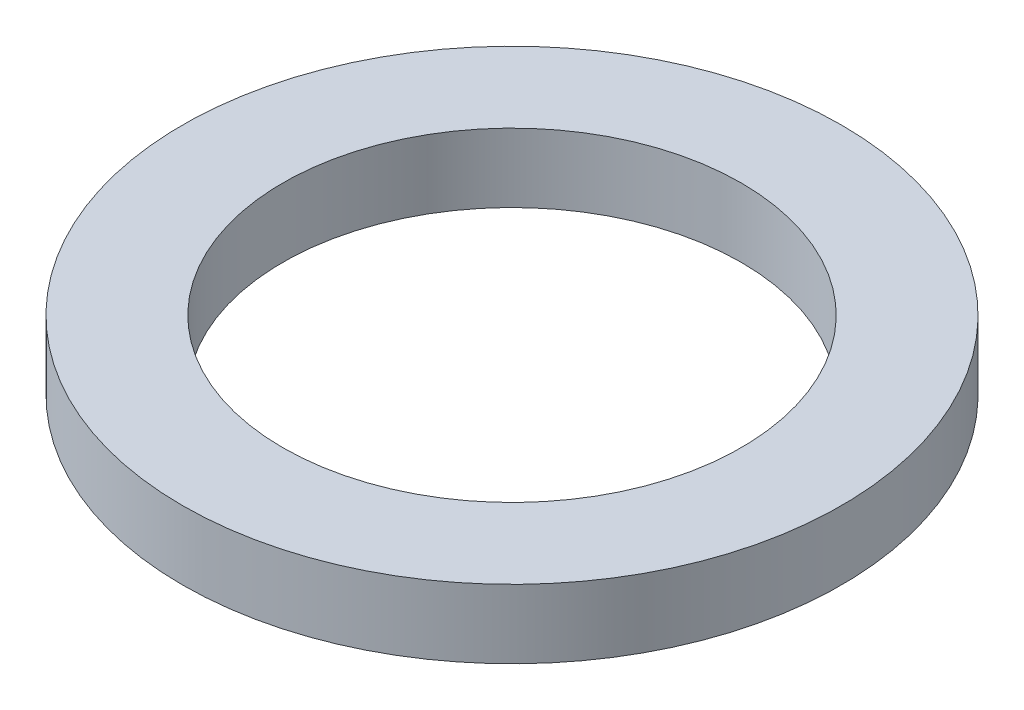
SolidWorks part; units mm, degrees
material "ABS"
ref_plane "Front Plane" through (0, 0, 0) normal (0, 0, 1) x (1, 0, 0)
ref_plane "Top Plane" through (0, 0, 0) normal (0, 1, 0) x (1, 0, 0)
ref_plane "Right Plane" through (0, 0, 0) normal (1, 0, 0) x (0, 0, -1)
sketch "Sketch1" plane through (0, 0, 0) normal (0, 1, 0) x (1, 0, 0)
  circle A0 centre (0, 0) radius 5.75
  circle A1 centre (0, 0) radius 4
  dimension "D1" = 11.5
  dimension "D2" = 8
extrude "Boss-Extrude1" add sketch "Sketch1" along normal blind 1.2
